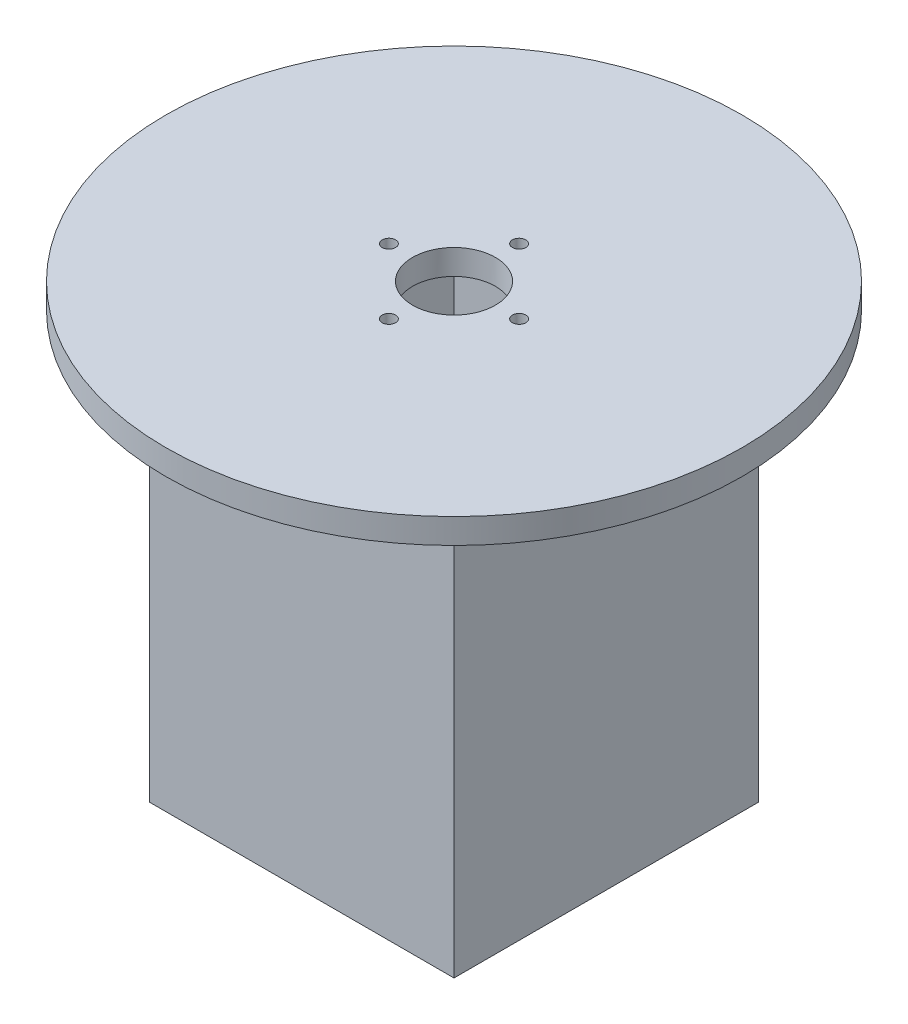
SolidWorks part; units mm, degrees
material "ABS_rapid_prototype"
ref_plane "Front Plane" through (0, 0, 0) normal (0, 0, 1) x (1, 0, 0)
ref_plane "Top Plane" through (0, 0, 0) normal (0, 1, 0) x (1, 0, 0)
ref_plane "Right Plane" through (0, 0, 0) normal (1, 0, 0) x (0, 0, -1)
sketch "Sketch1" plane through (0, 0, 0) normal (0, 0, 1) x (1, 0, 0)
  line L1 (0, 0) -> (77.2, 0)
  line L2 (0, 0) -> (0, 114.3)
  line L3 (0, 114.3) -> (77.2, 114.3)
  line L4 (77.2, 0) -> (77.2, 114.3)
  dimension "D1" = 114.3
  dimension "D2" = 77.2
extrude "Boss-Extrude1" add sketch "Sketch1" against normal blind 77.2
sketch "Sketch2" plane through (0, 0, 0) normal (0, -1, 0) x (1, 0, 0)
  line L0 (0, 0) -> (77.2, 0) construction
  line L1 (3.31, -3.31) -> (73.89, -3.31)
  line L2 (3.31, -3.31) -> (3.31, -73.89)
  line L3 (3.31, -73.89) -> (73.89, -73.89)
  line L4 (73.89, -3.31) -> (73.89, -73.89)
  line L5 (0, -77.2) -> (77.2, -77.2) construction
  line L6 (0, -77.2) -> (0, 0) construction
  line L7 (77.2, -77.2) -> (77.2, 0) construction
  dimension "D1" = 3.31
  dimension "D2" = 3.31
  dimension "D3" = 3.31
  dimension "D4" = 3.31
extrude "Cut-Extrude1" cut sketch "Sketch2" against normal blind 107.95
ref_plane "Plane1" through (0, 0, 0) normal (1, 0, 0) x (0, 0, -1)
sketch "Sketch3" plane through (0, 114.3, 0) normal (0, 1, 0) x (1, 0, 0)
  line L0 (77.2, 77.2) -> (0, 77.2) construction
  line L1 (0, 77.2) -> (0, 0) construction
  circle A0 centre (38.6, 38.6) radius 10.5
  circle A1 centre (38.6, 55.1) radius 1.7
  circle A2 centre (55.1, 38.6) radius 1.7
  circle A3 centre (38.6, 22.1) radius 1.7
  circle A4 centre (22.1, 38.6) radius 1.7
  dimension "D1" = 21
  dimension "D4" = 3.4
  dimension "D5" = 3.4
  dimension "D6" = 3.4
  dimension "D7" = 3.4
  dimension "D2" = 38.6
  dimension "D3" = 38.6
  dimension "D8" = 16.5
  dimension "D9" = 16.5
  dimension "D10" = 16.5
  dimension "D11" = 16.5
extrude "Cut-Extrude2" cut sketch "Sketch3" against normal through all
sketch "Sketch4" plane through (0, 114.3, 0) normal (0, 1, 0) x (1, 0, 0)
  circle A0 centre (38.6, 38.6) radius 73.025
  circle A1 centre (38.6, 55.1) radius 1.7
  circle A2 centre (55.1, 38.6) radius 1.7
  circle A3 centre (38.6, 22.1) radius 1.7
  circle A4 centre (22.1, 38.6) radius 1.7
  circle A5 centre (38.6, 38.6) radius 10.5
  dimension "D1" = 146.05
  dimension "D2" = 3.4
extrude "Boss-Extrude4" add sketch "Sketch4" against normal blind 6.35
